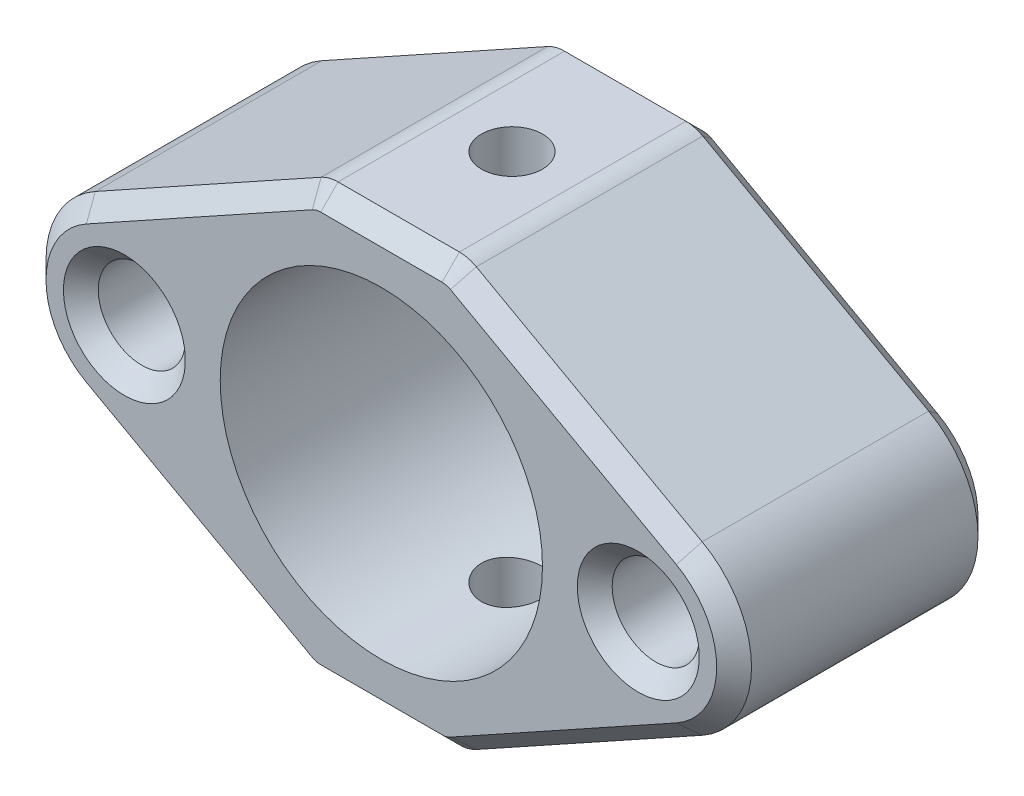
SolidWorks part; units mm, degrees
ref_plane "正面(Front)" through (0, 0, 0) normal (0, 0, 1) x (1, 0, 0)
ref_plane "平面(Top)" through (0, 0, 0) normal (0, 1, 0) x (1, 0, 0)
ref_plane "右側面(Right)" through (0, 0, 0) normal (1, 0, 0) x (0, 0, -1)
sketch "ｽｹｯﾁ1" plane through (0, 0, 0) normal (0, 0, 1) x (1, 0, 0)
  line L0 (0, 0) -> (0, 47.4525) construction
  line L1 (0, 0) -> (65.7266, 0) construction
  line L2 (4, 12.25) -> (17.4172, 4.81)
  line L3 (4, -12.25) -> (17.4172, -4.81)
  line L4 (-4, -12.25) -> (-17.4172, -4.81)
  line L5 (-4, 12.25) -> (-17.4172, 4.81)
  line L6 (4, 12.25) -> (-4, 12.25)
  line L7 (4, -12.25) -> (-4, -12.25)
  circle A0 centre (0, 0) radius 9.25
  circle A1 centre (14.75, 0) radius 2.5
  arc A3 (17.4172, 4.81) -> (17.4172, -4.81) centre (14.75, 0) cw
  arc A5 (-17.4172, 4.81) -> (-17.4172, -4.81) centre (-14.75, 0) ccw
  circle A6 centre (-14.75, 0) radius 2.5
  point P18 (9.1624, 9.8379)
  point P19 (4.0218, 12)
  point P22 (0, 0)
  point P23 (0, 12.25)
  point P25 (0, -12.25)
  point P26 (0, 0)
  point P27 (0, 0)
  point P28 (5.5332, 12)
  point P29 (5.7352, 12)
  dimension "D1" = 18.5
  dimension "D2" = 5
  dimension "D3" = 3
  dimension "D4" = 3
  dimension "D5" = 3
  dimension "D6" = 8
extrude "ﾎﾞｽ - 押し出し1" add sketch "ｽｹｯﾁ1" along normal mid plane 15
sketch "ｽｹｯﾁ3" plane through (0, 0, 0) normal (0, 1, 0) x (1, 0, 0)
  circle A0 centre (0, 0) radius 1.75
  dimension "D1" = 3.5
extrude "ｶｯﾄ - 押し出し1" cut sketch "ｽｹｯﾁ3" against normal through all both and the other way through all
chamfer "面取り1" distance 1 angle 45 4 edges at (-17.25, 0, -7.5) (17.25, 0, -7.5) (17.25, 0, 7.5) (-17.25, 0, 7.5)
fillet "ﾌｨﾚｯﾄ1" radius 2 4 edges at (4, -12.25, 0) (-4, -12.25, 0) (4, 12.25, 0) (-4, 12.25, 0)
chamfer "面取り2" distance 1 angle 45 24 edges at (10.9348, 8.4045, -7.5) (20.25, 0, -7.5) (-10.9348, 8.4045, -7.5) (10.9348, -8.4045, -7.5) (-20.25, 0, -7.5) (-10.9348, -8.4045, -7.5) (10.9348, 8.4045, 7.5) (20.25, 0, 7.5) (-10.9348, 8.4045, 7.5) (10.9348, -8.4045, 7.5) (-20.25, 0, 7.5) (-10.9348, -8.4045, 7.5) (0, -12.25, -7.5) (3.9835, 12.1863, -7.5) (0, 12.25, -7.5) (-3.9835, 12.1863, -7.5) (3.9835, -12.1863, -7.5) (-3.9835, -12.1863, -7.5) (3.9835, 12.1863, 7.5) (0, 12.25, 7.5) (-3.9835, 12.1863, 7.5) (3.9835, -12.1863, 7.5) (0, -12.25, 7.5) (-3.9835, -12.1863, 7.5)
